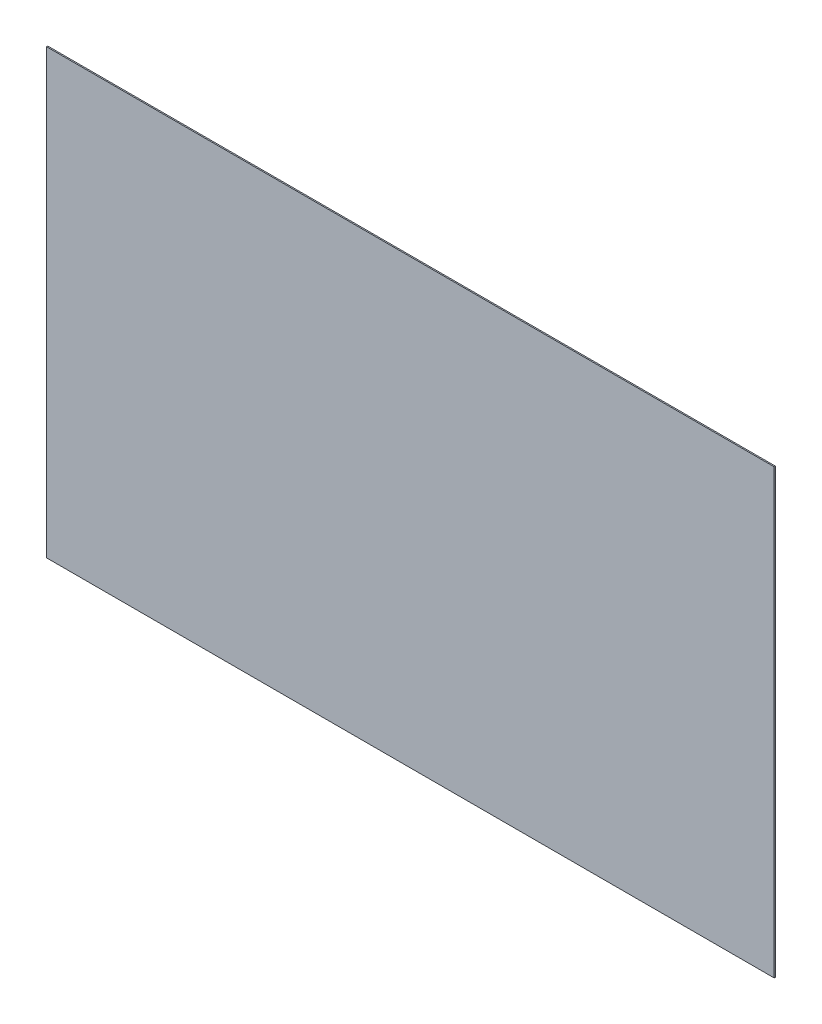
SolidWorks part; units mm, degrees
ref_plane "Alzado" through (0, 0, 0) normal (0, 0, 1) x (1, 0, 0)
ref_plane "Planta" through (0, 0, 0) normal (0, 1, 0) x (1, 0, 0)
ref_plane "Vista lateral" through (0, 0, 0) normal (1, 0, 0) x (0, 0, -1)
sketch "Croquis1" plane through (0, 0, 0) normal (0, 0, 1) x (1, 0, 0)
  line L1 (-3000, 1825) -> (3000, 1825)
  line L2 (-3000, 1825) -> (-3000, -1825)
  line L3 (-3000, -1825) -> (3000, -1825)
  line L4 (3000, 1825) -> (3000, -1825)
  line L5 (-3000, 1825) -> (3000, -1825) construction
  line L6 (-3000, -1825) -> (3000, 1825) construction
  point P0 (0, 0)
  dimension "D1" = 6000
  dimension "D2" = 3650
extrude "Saliente-Extruir1" add sketch "Croquis1" along normal blind 10
